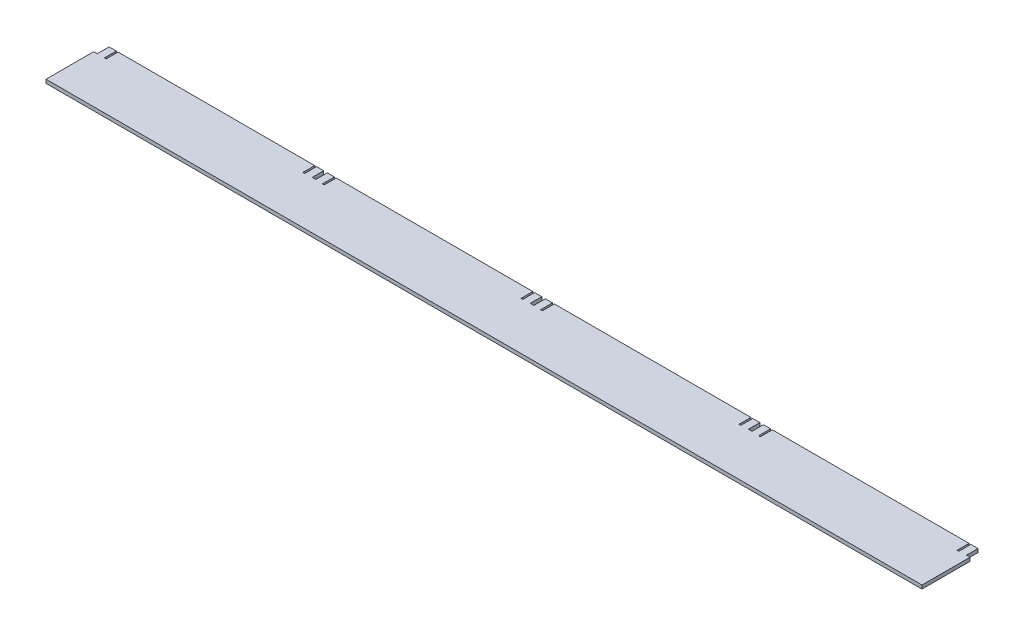
SolidWorks part; units mm, degrees
ref_plane "Front Plane" through (0, 0, 0) normal (0, 0, 1) x (1, 0, 0)
ref_plane "Top Plane" through (0, 0, 0) normal (0, 1, 0) x (1, 0, 0)
ref_plane "Right Plane" through (0, 0, 0) normal (1, 0, 0) x (0, 0, -1)
sketch "Sketch1" plane through (0, 0, 0) normal (0, 1, 0) x (1, 0, 0)
  line L0 (-84, 25) -> (-84, 15)
  line L1 (-90, -25) -> (90, -25)
  line L2 (-90, -25) -> (-90, 25)
  line L3 (-90, 25) -> (-84, 25)
  line L4 (90, -25) -> (90, 25)
  line L5 (-84, 15) -> (-82.5, 15)
  line L6 (-82.5, 15) -> (-82.5, 25)
  line L7 (82.5, 25) -> (82.5, 15)
  line L8 (82.5, 15) -> (84, 15)
  line L9 (84, 15) -> (84, 25)
  line L10 (-82.5, 25) -> (82.5, 25)
  line L11 (84, 25) -> (90, 25)
  point P4 (-90, 0)
  point P5 (0, 25)
  dimension "D1" = 50
  dimension "D2" = 180
  dimension "D3" = 6
  dimension "D4" = 1.5
  dimension "D5" = 10
extrude "Boss-Extrude1" add sketch "Sketch1" along normal mid plane 3
sketch "Sketch2" plane through (0, 0, 0) normal (0, 1, 0) x (1, 0, 0)
  line L0 (90, -25) -> (90, 25) construction
  line L1 (90, 15.3314) -> (93, 15.3314)
  line L2 (90, 15.3314) -> (90, -25)
  line L3 (90, -25) -> (93, -25)
  line L4 (93, 15.3314) -> (93, -25)
  line L5 (-90, -25) -> (90, -25) construction
  dimension "D1" = 3
extrude "Boss-Extrude2" add sketch "Sketch2" along normal mid plane 3
pattern_linear "LPattern2" count 4 spacing 183 along (1, 0, 0) of "Boss-Extrude1", "Boss-Extrude2"
sketch "Sketch3" plane through (0, 0, 0) normal (0, 1, 0) x (1, 0, 0)
  line L0 (-90, 25) -> (-90, -25) construction
  line L1 (-90, 15) -> (-93, 15)
  line L2 (-90, 15) -> (-90, -25)
  line L3 (-90, -25) -> (-93, -25)
  line L4 (-93, 15) -> (-93, -25)
  line L5 (-82.5, 15) -> (-84, 15) construction
  dimension "D1" = 3
extrude "Boss-Extrude3" add sketch "Sketch3" along normal mid plane 3
equation "\"mdfWidth\"= 3"
equation "\"cellSide\"= 180"
equation "\"mazeHeight\"= 50"
equation "\"slitHeight\"= 10"
equation "\"slitWidth\"= \"wallThickness\""
equation "\"gripWidth\"= 6"
equation "\"wallThickness\"= 1.5"
equation "\"D1@Sketch1\"= \"mazeHeight\""
equation "\"D2@Sketch1\"= \"cellSide\""
equation "\"D3@Sketch1\"= \"gripWidth\""
equation "\"D4@Sketch1\"= \"wallThickness\""
equation "\"D5@Sketch1\"= \"slitHeight\""
equation "\"D1@Boss-Extrude1\"= \"mdfWidth\""
equation "\"D1@Sketch2\"= \"mdfWidth\""
equation "\"D1@Boss-Extrude2\"= \"mdfWidth\""
equation "\"D1@LPattern1\"= 2"
equation "\"D3@LPattern1\"= \"cellSide\" + \"mdfWidth\""
equation "\"nbUnits\"=4"
equation "\"D1@LPattern2\"= \"nbUnits\""
equation "\"D1@Sketch3\"= \"mdfWidth\""
equation "\"D1@Boss-Extrude3\"= \"mdfWidth\""
equation "\"D3@LPattern2\"= \"cellSide\" + \"mdfWidth\""
